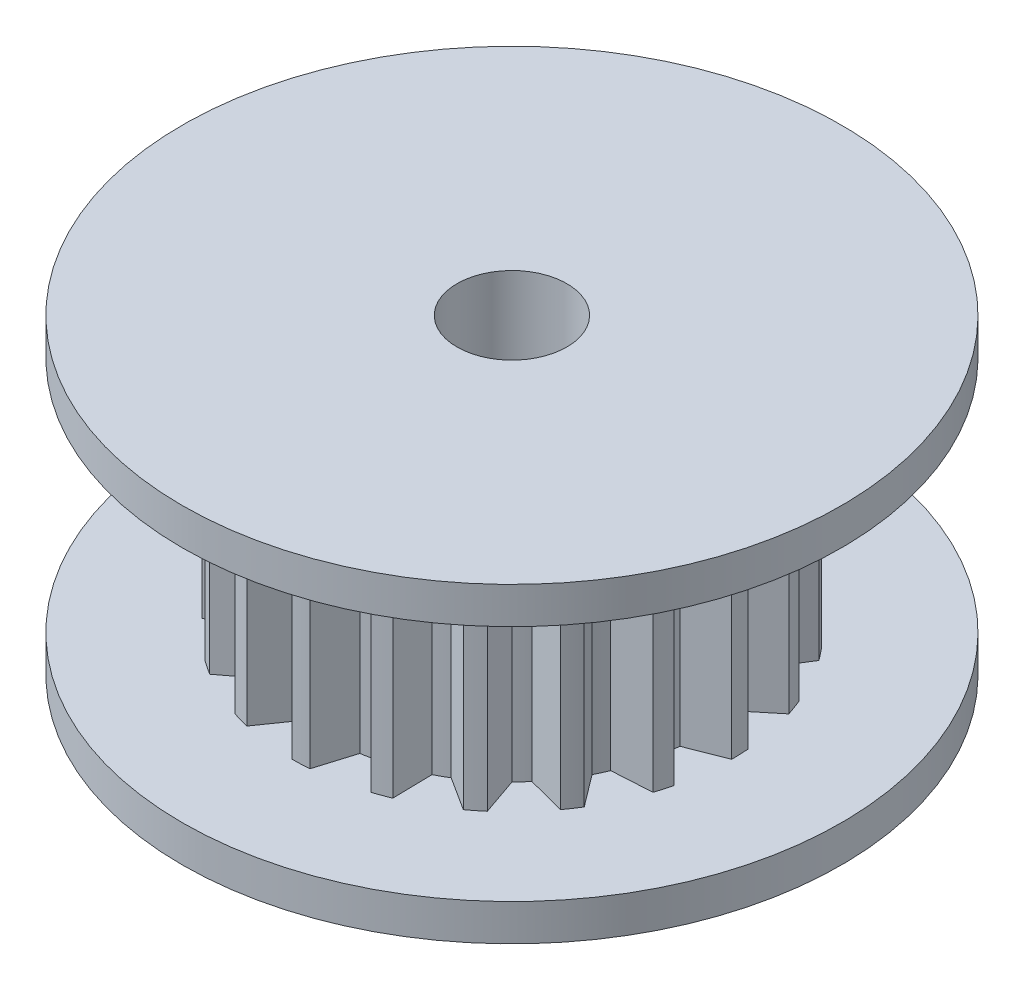
SolidWorks part; units mm, degrees
ref_plane "前视基准面" through (0, 0, 0) normal (0, 0, 1) x (1, 0, 0)
ref_plane "上视基准面" through (0, 0, 0) normal (0, 1, 0) x (1, 0, 0)
ref_plane "右视基准面" through (0, 0, 0) normal (1, 0, 0) x (0, 0, -1)
sketch "草图1" plane through (0, 0, 0) normal (0, 1, 0) x (1, 0, 0)
  circle A0 centre (0, 0) radius 9
  dimension "D1" = 18
extrude "凸台-拉伸1" add sketch "草图1" along normal blind 1
sketch "草图2" plane through (0, 1, 0) normal (0, 1, 0) x (1, 0, 0)
  circle A0 centre (0, 0) radius 6
  dimension "D1" = 12
extrude "凸台-拉伸2" add sketch "草图2" along normal blind 6.5
sketch "草图3" plane through (0, 7.5, 0) normal (0, 1, 0) x (1, 0, 0)
  circle A0 centre (0, 0) radius 9
  dimension "D1" = 18
extrude "凸台-拉伸3" add sketch "草图3" along normal blind 1
sketch "草图4" plane through (0, 8.5, 0) normal (0, 1, 0) x (1, 0, 0)
  circle A0 centre (0, 0) radius 1.5
  dimension "D1" = 3
extrude "切除-拉伸1" cut sketch "草图4" against normal through all
sketch "草图5" plane through (0, 1, 0) normal (0, 1, 0) x (1, 0, 0)
  line L60 (-6, 0) -> (-4.9841, 0.3986)
  line L61 (-5.9819, -0.4662) -> (-4.9382, -0.7837)
  line L82 (-5.8331, 1.4052) -> (-4.9387, 0.7807)
  line L83 (-5.7063, 1.8541) -> (-4.617, 1.9192)
  line L84 (-5.1134, 3.1389) -> (-4.4557, 2.2686)
  line L85 (-4.8541, 3.5267) -> (-3.7979, 3.252)
  line L86 (-3.8932, 4.5654) -> (-3.5366, 3.5345)
  line L87 (-3.5267, 4.8541) -> (-2.6071, 4.2665)
  line L88 (-2.2918, 5.545) -> (-2.2713, 4.4543)
  line L89 (-1.8541, 5.7063) -> (-1.1611, 4.8633)
  line L90 (-0.4662, 5.9819) -> (-0.7837, 4.9382)
  line L91 (0, 6) -> (0.3986, 4.9841)
  line L92 (1.4052, 5.8331) -> (0.7807, 4.9387)
  line L93 (1.8541, 5.7063) -> (1.9192, 4.617)
  line L94 (3.1389, 5.1134) -> (2.2686, 4.4557)
  line L95 (3.5267, 4.8541) -> (3.252, 3.7979)
  line L96 (4.5654, 3.8932) -> (3.5345, 3.5366)
  line L97 (4.8541, 3.5267) -> (4.2665, 2.6071)
  line L98 (5.545, 2.2918) -> (4.4543, 2.2713)
  line L99 (5.7063, 1.8541) -> (4.8633, 1.1611)
  line L100 (5.9819, 0.4662) -> (4.9382, 0.7837)
  line L101 (6, 0) -> (4.9841, -0.3986)
  line L102 (5.8331, -1.4052) -> (4.9387, -0.7807)
  line L103 (5.7063, -1.8541) -> (4.617, -1.9192)
  line L104 (5.1134, -3.1389) -> (4.4557, -2.2686)
  line L105 (4.8541, -3.5267) -> (3.7979, -3.252)
  line L106 (3.8932, -4.5654) -> (3.5366, -3.5345)
  line L107 (3.5267, -4.8541) -> (2.6071, -4.2665)
  line L108 (2.2918, -5.545) -> (2.2713, -4.4543)
  line L109 (1.8541, -5.7063) -> (1.1611, -4.8633)
  line L110 (0.4662, -5.9819) -> (0.7837, -4.9382)
  line L111 (0, -6) -> (-0.3986, -4.9841)
  line L112 (-1.4052, -5.8331) -> (-0.7807, -4.9387)
  line L113 (-1.8541, -5.7063) -> (-1.9192, -4.617)
  line L114 (-3.1389, -5.1134) -> (-2.2686, -4.4557)
  line L115 (-3.5267, -4.8541) -> (-3.252, -3.7979)
  line L116 (-4.5654, -3.8932) -> (-3.5345, -3.5366)
  line L117 (-4.8541, -3.5267) -> (-4.2665, -2.6071)
  line L118 (-5.545, -2.2918) -> (-4.4543, -2.2713)
  line L119 (-5.7063, -1.8541) -> (-4.8633, -1.1611)
  arc A2 (-4.9382, -0.7837) -> (-4.8633, -1.1611) centre (0, 0) ccw
  arc A3 (-5.9819, -0.4662) -> (-5.7063, -1.8541) centre (0, 0) ccw
  arc A4 (-4.9387, 0.7807) -> (-4.9841, 0.3986) centre (0, 0) ccw
  arc A5 (-4.4557, 2.2686) -> (-4.617, 1.9192) centre (0, 0) ccw
  arc A6 (-3.5366, 3.5345) -> (-3.7979, 3.252) centre (0, 0) ccw
  arc A7 (-2.2713, 4.4543) -> (-2.6071, 4.2665) centre (0, 0) ccw
  arc A8 (-0.7837, 4.9382) -> (-1.1611, 4.8633) centre (0, 0) ccw
  arc A9 (0.7807, 4.9387) -> (0.3986, 4.9841) centre (0, 0) ccw
  arc A10 (2.2686, 4.4557) -> (1.9192, 4.617) centre (0, 0) ccw
  arc A11 (3.5345, 3.5366) -> (3.252, 3.7979) centre (0, 0) ccw
  arc A12 (4.4543, 2.2713) -> (4.2665, 2.6071) centre (0, 0) ccw
  arc A13 (4.9382, 0.7837) -> (4.8633, 1.1611) centre (0, 0) ccw
  arc A14 (4.9387, -0.7807) -> (4.9841, -0.3986) centre (0, 0) ccw
  arc A15 (4.4557, -2.2686) -> (4.617, -1.9192) centre (0, 0) ccw
  arc A16 (3.5366, -3.5345) -> (3.7979, -3.252) centre (0, 0) ccw
  arc A17 (2.2713, -4.4543) -> (2.6071, -4.2665) centre (0, 0) ccw
  arc A18 (0.7837, -4.9382) -> (1.1611, -4.8633) centre (0, 0) ccw
  arc A19 (-0.7807, -4.9387) -> (-0.3986, -4.9841) centre (0, 0) ccw
  arc A20 (-2.2686, -4.4557) -> (-1.9192, -4.617) centre (0, 0) ccw
  arc A21 (-3.5345, -3.5366) -> (-3.252, -3.7979) centre (0, 0) ccw
  arc A22 (-4.4543, -2.2713) -> (-4.2665, -2.6071) centre (0, 0) ccw
  arc A23 (-5.8331, 1.4052) -> (-6, 0) centre (0, 0) ccw
  arc A24 (-5.1134, 3.1389) -> (-5.7063, 1.8541) centre (0, 0) ccw
  arc A25 (-3.8932, 4.5654) -> (-4.8541, 3.5267) centre (0, 0) ccw
  arc A26 (-2.2918, 5.545) -> (-3.5267, 4.8541) centre (0, 0) ccw
  arc A27 (-0.4662, 5.9819) -> (-1.8541, 5.7063) centre (0, 0) ccw
  arc A28 (1.4052, 5.8331) -> (0, 6) centre (0, 0) ccw
  arc A29 (3.1389, 5.1134) -> (1.8541, 5.7063) centre (0, 0) ccw
  arc A30 (4.5654, 3.8932) -> (3.5267, 4.8541) centre (0, 0) ccw
  arc A31 (5.545, 2.2918) -> (4.8541, 3.5267) centre (0, 0) ccw
  arc A32 (5.9819, 0.4662) -> (5.7063, 1.8541) centre (0, 0) ccw
  arc A33 (5.8331, -1.4052) -> (6, 0) centre (0, 0) ccw
  arc A34 (5.1134, -3.1389) -> (5.7063, -1.8541) centre (0, 0) ccw
  arc A35 (3.8932, -4.5654) -> (4.8541, -3.5267) centre (0, 0) ccw
  arc A36 (2.2918, -5.545) -> (3.5267, -4.8541) centre (0, 0) ccw
  arc A37 (0.4662, -5.9819) -> (1.8541, -5.7063) centre (0, 0) ccw
  arc A38 (-1.4052, -5.8331) -> (0, -6) centre (0, 0) ccw
  arc A39 (-3.1389, -5.1134) -> (-1.8541, -5.7063) centre (0, 0) ccw
  arc A40 (-4.5654, -3.8932) -> (-3.5267, -4.8541) centre (0, 0) ccw
  arc A41 (-5.545, -2.2918) -> (-4.8541, -3.5267) centre (0, 0) ccw
  point P30 (0, 0)
  point P171 (0, 0)
  dimension "D1" = 10
  dimension "D2" = 6
  dimension "D3" = 20
extrude "切除-拉伸2" cut sketch "草图5" along normal blind 6.5
